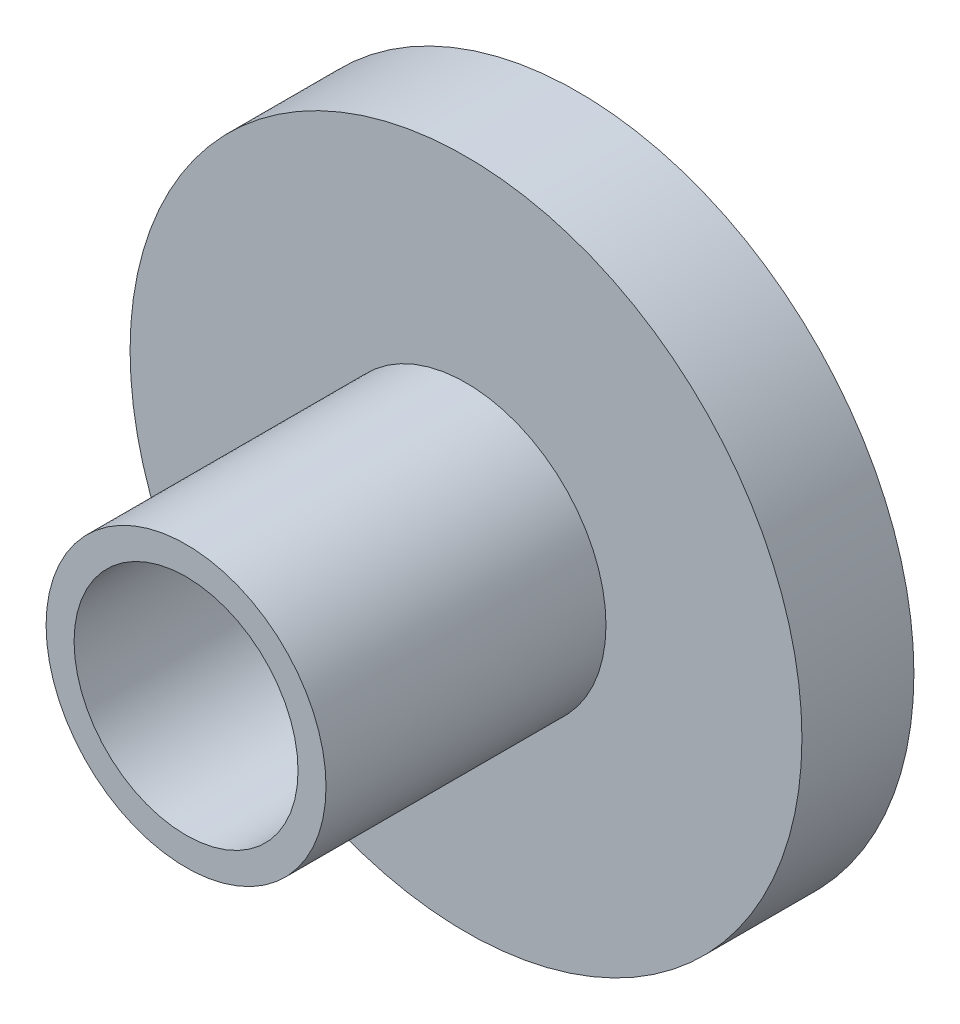
SolidWorks part; units mm, degrees
ref_plane "前视基准面" through (0, 0, 0) normal (0, 0, 1) x (1, 0, 0)
ref_plane "上视基准面" through (0, 0, 0) normal (0, 1, 0) x (1, 0, 0)
ref_plane "右视基准面" through (0, 0, 0) normal (1, 0, 0) x (0, 0, -1)
sketch "草图1" plane through (0, 0, 0) normal (0, 0, 1) x (1, 0, 0)
  circle A0 centre (0, 0) radius 6
extrude "凸台-拉伸1" add sketch "草图1" along normal blind 2
sketch "草图2" plane through (0, 0, 2) normal (0, 0, 1) x (1, 0, 0)
  circle A0 centre (0, 0) radius 2
  circle A1 centre (0, 0) radius 2.5
extrude "凸台-拉伸2" add sketch "草图2" along normal blind 5
